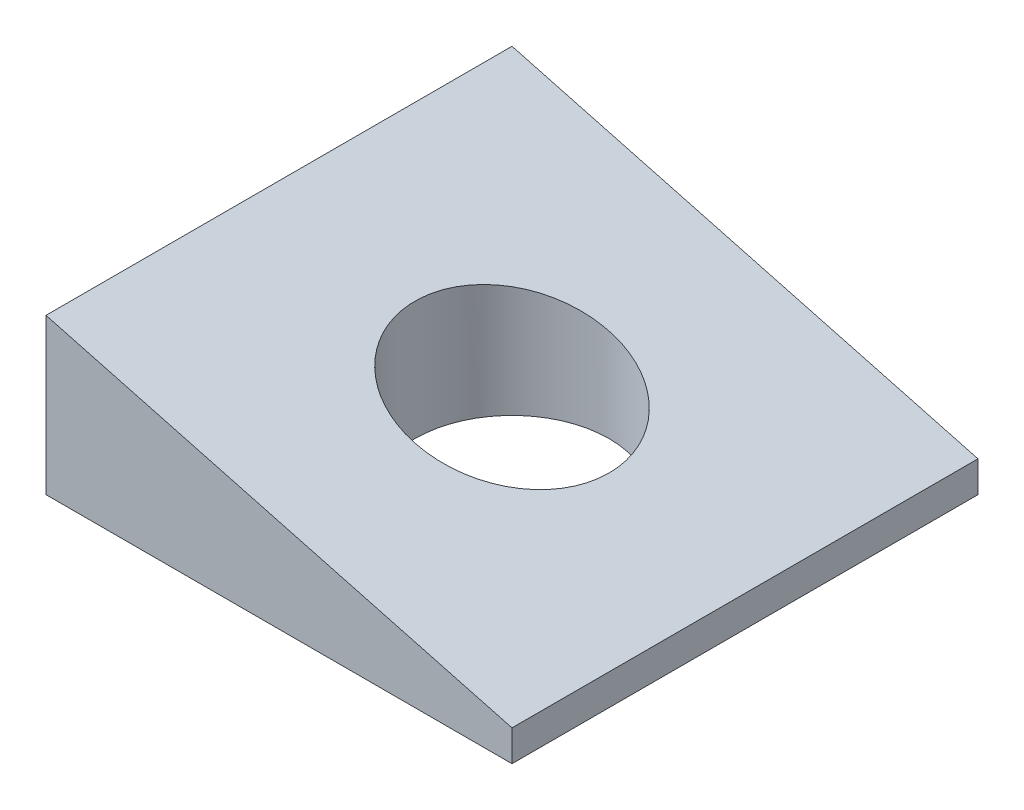
SolidWorks part; units mm, degrees
material "ASTM A36 Steel"
ref_plane "Front Plane" through (0, 0, 0) normal (0, 0, 1) x (1, 0, 0)
ref_plane "Top Plane" through (0, 0, 0) normal (0, 1, 0) x (1, 0, 0)
ref_plane "Right Plane" through (0, 0, 0) normal (1, 0, 0) x (0, 0, -1)
sketch "Sketch1" plane through (0, 0, 0) normal (0, 0, 1) x (1, 0, 0)
  line L0 (0, 0) -> (0, 12.7)
  line L1 (0, 12.7) -> (38.1, 2.54)
  line L2 (38.1, 2.54) -> (38.1, 0)
  line L3 (38.1, 0) -> (0, 0)
  dimension "D1" = 2.54
  dimension "D2" = 12.7
  dimension "D3" = 38.1
extrude "Boss-Extrude1" add sketch "Sketch1" along normal blind 38.1
sketch "Sketch2" plane through (0, 0, 0) normal (0, -1, 0) x (1, 0, 0)
  line L0 (0, 38.1) -> (38.1, 38.1) construction
  line L1 (38.1, 38.1) -> (38.1, 0) construction
  circle A0 centre (19.05, 19.05) radius 7.9375
  dimension "D1" = 15.875
  dimension "D2" = 19.05
  dimension "D3" = 19.05
extrude "Cut-Extrude1" cut sketch "Sketch2" against normal blind 38.1
